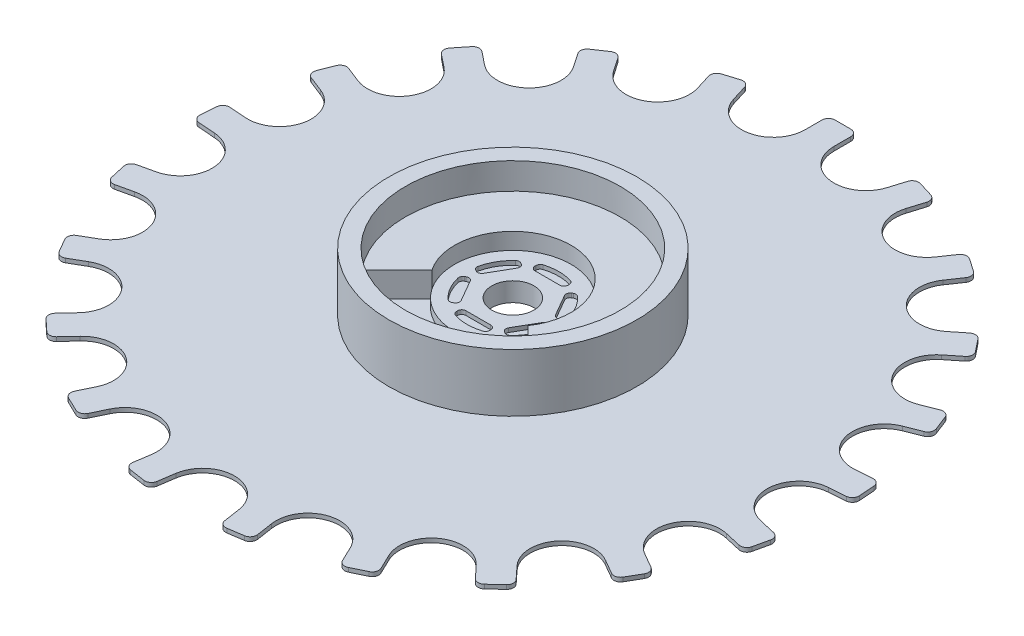
SolidWorks part; units mm, degrees
material "ABS"
ref_plane "Plano frontal" through (0, 0, 0) normal (0, 0, 1) x (1, 0, 0)
ref_plane "Plano superior" through (0, 0, 0) normal (0, 1, 0) x (1, 0, 0)
ref_plane "Plano direito" through (0, 0, 0) normal (1, 0, 0) x (0, 0, -1)
sketch "Esboço1" plane through (0, 0, 0) normal (0, -1, 0) x (1, 0, 0)
  line L0 (-1.745, -0.8) -> (-1.745, 0) construction
  line L1 (-0.945, 0) -> (0.945, 0)
  line L2 (-1.745, -0.8) -> (-1.745, -39.142)
  line L3 (-0.945, -39.942) -> (0.945, -39.942)
  line L4 (1.745, -0.8) -> (1.745, -39.142)
  line L5 (-0.945, 0) -> (-1.745, 0) construction
  arc A0 (0.945, 0) -> (1.745, -0.8) centre (0.945, -0.8) cw
  arc A1 (-0.945, 0) -> (-1.745, -0.8) centre (-0.945, -0.8) ccw
  arc A2 (0.945, -39.942) -> (1.745, -39.142) centre (0.945, -39.142) ccw
  arc A3 (-1.745, -39.142) -> (-0.945, -39.942) centre (-0.945, -39.142) ccw
  point P4 (0, 0)
  point P8 (1.745, 0)
  point P11 (-1.745, 0)
  point P14 (1.745, -39.942)
  dimension "D3" = 0.8
  dimension "D4" = 0.8
  dimension "D1" = 3.49
  dimension "D2" = 39.942
extrude "Ressalto-extrusão1" add sketch "Esboço1" along normal mid plane 0.5
sketch "Esboço2" plane through (0, 0, 0) normal (0, 1, 0) x (1, 0, 0)
  line L0 (-1.745, 0.8) -> (-1.745, 39.142) construction
  circle A0 centre (0, 0) radius 1.745
extrude "Ressalto-extrusão2" add sketch "Esboço2" along normal blind 4.625
pattern_circular "PadrãoCircular1" count 21 over 360 about axis through (0, 0, 0) along (0, 1, 0) of "Ressalto-extrusão1"
fillet "Fillet2" radius 3.85 21 edges at (0, 0, 11.7081) (3.451, 0, 11.1879) (6.5954, 0, 9.6737) (10.8988, 0, 4.2774) (9.1538, 0, 7.2999) (11.6754, 0, 0.8749) (11.4145, 0, -2.6053) (10.1395, 0, -5.854) (7.9635, 0, -8.5826) (5.0799, 0, -10.5486) (1.745, 0, -11.5773) (-1.745, 0, -11.5773) (-5.0799, 0, -10.5486) (-7.9635, 0, -8.5826) (-10.1395, 0, -5.854) (-11.4145, 0, -2.6053) (-11.6754, 0, 0.8749) (-10.8988, 0, 4.2774) (-9.1538, 0, 7.2999) (-6.5954, 0, 9.6737) (-3.451, 0, 11.1879)
sketch "Sketch2" plane through (0, 0.25, 0) normal (0, 1, 0) x (1, 0, 0)
  circle A0 centre (0, 0) radius 15
  dimension "D1" = 30
extrude "Boss-Extrude1" add sketch "Sketch2" along normal blind 7
sketch "Sketch4" plane through (0, 7.25, 0) normal (0, 1, 0) x (1, 0, 0)
  circle A0 centre (0, 0) radius 13
  circle A1 centre (0, 0) radius 15
  circle A2 centre (0, 0) radius 15 construction
  dimension "D1" = 0
  dimension "D2" = 2
extrude "Cut-Extrude2" cut sketch "Sketch4" against normal blind 6.2
sketch "Sketch7" plane through (0, 1.05, 0) normal (0, 1, 0) x (1, 0, 0)
  circle A0 centre (0, 0) radius 6.75 construction
  circle A1 centre (0, 0) radius 7.05
  dimension "D1" = 13.5
  dimension "D2" = 0.3
extrude "Boss-Extrude4" add sketch "Sketch7" along normal blind 1
sketch "Sketch9" plane through (0, 2.05, 0) normal (0, 1, 0) x (1, 0, 0)
  line L0 (-2, -4.8221) -> (-2, -4.6771)
  line L1 (-1.5, -4.1771) -> (1.5, -4.1771)
  line L2 (2, -4.6771) -> (2, -4.8221)
  line L18 (-5.176, -0.679) -> (-5.0505, -0.6065)
  line L19 (-4.3675, -0.7895) -> (-2.8675, -3.3876)
  line L20 (-3.0505, -4.0706) -> (-3.176, -4.1431)
  line L21 (-3.176, 4.1431) -> (-3.0505, 4.0706)
  line L22 (-2.8675, 3.3876) -> (-4.3675, 0.7895)
  line L23 (-5.0505, 0.6065) -> (-5.176, 0.679)
  line L24 (2, 4.8221) -> (2, 4.6771)
  line L25 (1.5, 4.1771) -> (-1.5, 4.1771)
  line L26 (-2, 4.6771) -> (-2, 4.8221)
  line L27 (5.176, 0.679) -> (5.0505, 0.6065)
  line L28 (4.3675, 0.7895) -> (2.8675, 3.3876)
  line L29 (3.0505, 4.0706) -> (3.176, 4.1431)
  line L30 (3.176, -4.1431) -> (3.0505, -4.0706)
  line L31 (2.8675, -3.3876) -> (4.3675, -0.7895)
  line L32 (5.0505, -0.6065) -> (5.176, -0.679)
  circle A1 centre (0, 0) radius 7.05
  circle A2 centre (0, 0) radius 7.05 construction
  circle A5 centre (0, 0) radius 5.55
  arc A6 (-1.6485, -5.2995) -> (1.6485, -5.2995) centre (0, 0) ccw
  arc A9 (2, -4.8221) -> (1.6485, -5.2995) centre (1.5, -4.8221) cw
  arc A10 (-2, -4.8221) -> (-1.6485, -5.2995) centre (-1.5, -4.8221) ccw
  arc A11 (1.5, -4.1771) -> (2, -4.6771) centre (1.5, -4.6771) cw
  arc A12 (-2, -4.6771) -> (-1.5, -4.1771) centre (-1.5, -4.6771) cw
  arc A13 (-5.4138, -1.2221) -> (-3.7653, -4.0774) centre (0, 0) ccw
  arc A14 (-3.176, -4.1431) -> (-3.7653, -4.0774) centre (-3.426, -3.7101) cw
  arc A15 (-5.176, -0.679) -> (-5.4138, -1.2221) centre (-4.926, -1.112) ccw
  arc A16 (-2.8675, -3.3876) -> (-3.0505, -4.0706) centre (-3.3005, -3.6376) cw
  arc A17 (-5.0505, -0.6065) -> (-4.3675, -0.7895) centre (-4.8005, -1.0395) cw
  arc A18 (-3.7653, 4.0774) -> (-5.4138, 1.2221) centre (0, 0) ccw
  arc A19 (-5.176, 0.679) -> (-5.4138, 1.2221) centre (-4.926, 1.112) cw
  arc A20 (-3.176, 4.1431) -> (-3.7653, 4.0774) centre (-3.426, 3.7101) ccw
  arc A21 (-4.3675, 0.7895) -> (-5.0505, 0.6065) centre (-4.8005, 1.0395) cw
  arc A22 (-3.0505, 4.0706) -> (-2.8675, 3.3876) centre (-3.3005, 3.6376) cw
  arc A23 (1.6485, 5.2995) -> (-1.6485, 5.2995) centre (0, 0) ccw
  arc A24 (-2, 4.8221) -> (-1.6485, 5.2995) centre (-1.5, 4.8221) cw
  arc A25 (2, 4.8221) -> (1.6485, 5.2995) centre (1.5, 4.8221) ccw
  arc A26 (-1.5, 4.1771) -> (-2, 4.6771) centre (-1.5, 4.6771) cw
  arc A27 (2, 4.6771) -> (1.5, 4.1771) centre (1.5, 4.6771) cw
  arc A28 (5.4138, 1.2221) -> (3.7653, 4.0774) centre (0, 0) ccw
  arc A29 (3.176, 4.1431) -> (3.7653, 4.0774) centre (3.426, 3.7101) cw
  arc A30 (5.176, 0.679) -> (5.4138, 1.2221) centre (4.926, 1.112) ccw
  arc A31 (2.8675, 3.3876) -> (3.0505, 4.0706) centre (3.3005, 3.6376) cw
  arc A32 (5.0505, 0.6065) -> (4.3675, 0.7895) centre (4.8005, 1.0395) cw
  arc A33 (3.7653, -4.0774) -> (5.4138, -1.2221) centre (0, 0) ccw
  arc A34 (5.176, -0.679) -> (5.4138, -1.2221) centre (4.926, -1.112) cw
  arc A35 (3.176, -4.1431) -> (3.7653, -4.0774) centre (3.426, -3.7101) ccw
  arc A36 (4.3675, -0.7895) -> (5.0505, -0.6065) centre (4.8005, -1.0395) cw
  arc A37 (3.0505, -4.0706) -> (2.8675, -3.3876) centre (3.3005, -3.6376) cw
  point P6 (0, -4.1771)
  point P35 (-2, -5.1771)
  point P38 (2, -4.1771)
  point P41 (-2, -4.1771)
  point P84 (0, 0)
  dimension "D6" = 0.5
  dimension "D3" = 1
  dimension "D4" = 4
  dimension "D1" = 0
  dimension "D2" = 1.5
extrude "Cut-Extrude3" cut sketch "Sketch9" against normal blind 0.5
sketch "Sketch8" plane through (0, 1.05, 0) normal (0, 1, 0) x (1, 0, 0)
  line L0 (-10.0507, -8.2453) -> (-5.8054, -4)
  line L1 (0, -6.875) -> (0, 6.875) construction
  line L2 (10.0507, -8.2453) -> (5.8054, -4)
  circle A1 centre (0, 0) radius 7.05
  arc A2 (5.8054, -4) -> (-5.8054, -4) centre (0, 0) ccw
  circle A3 centre (0, 0) radius 7.05 construction
  circle A4 centre (0, 0) radius 13 construction
  circle A6 centre (0, 0) radius 13
  arc A7 (10.0507, -8.2453) -> (-10.0507, -8.2453) centre (0, 0) ccw
  dimension "D3" = 270
  dimension "D4" = 4
  dimension "D1" = 0
  dimension "D2" = 0
extrude "Boss-Extrude5" add sketch "Sketch8" along normal offset from surface (3 mm away) 2 up to face at (-4.1256, 2.05, 2.3819) offset beyond the face yes
sketch "Sketch3" plane through (0, 0, 0) normal (0, 1, 0) x (1, 0, 0)
  circle A0 centre (0, 0) radius 2 construction
  circle A1 centre (0, 0) radius 2.55
  dimension "D1" = 4
  dimension "D2" = 0.55
extrude "Cut-Extrude1" cut sketch "Sketch3" against normal through all both and the other way through all
